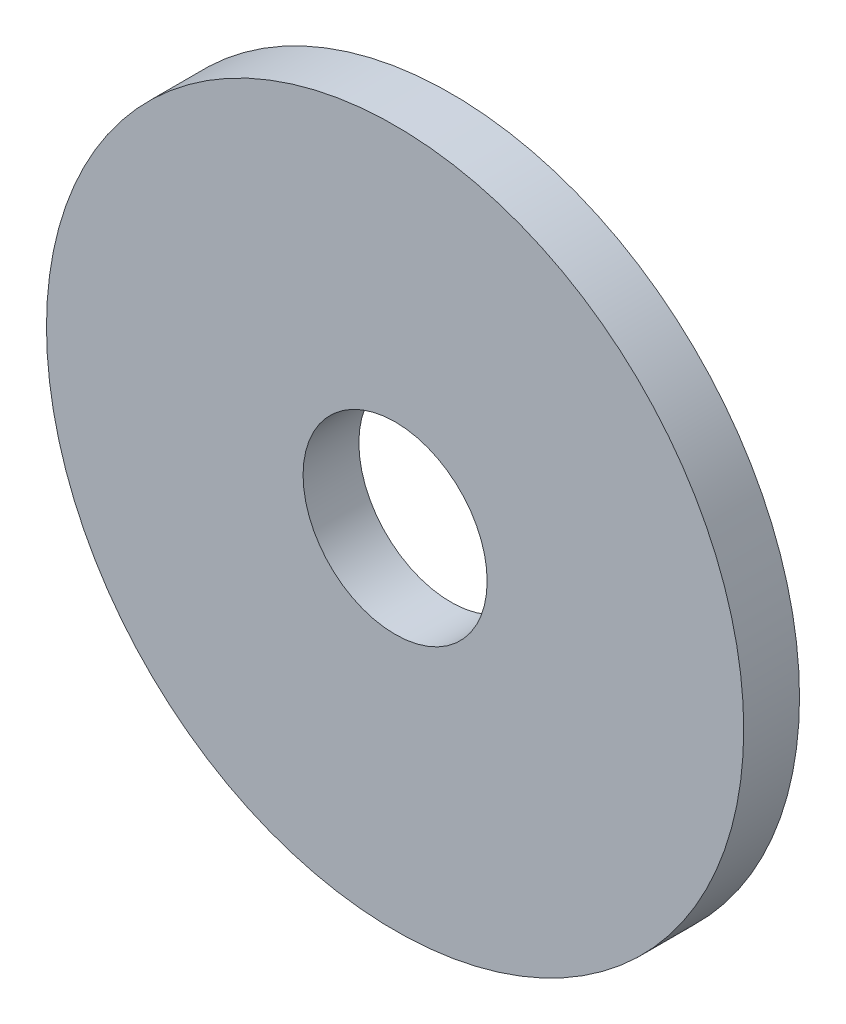
SolidWorks part; units mm, degrees
ref_plane "Plan de face" through (0, 0, 0) normal (0, 0, 1) x (1, 0, 0)
ref_plane "Plan de dessus" through (0, 0, 0) normal (0, 1, 0) x (1, 0, 0)
ref_plane "Plan de droite" through (0, 0, 0) normal (1, 0, 0) x (0, 0, -1)
sketch "Esquisse1" plane through (0, 0, 0) normal (0, 0, 1) x (1, 0, 0)
  circle A0 centre (0, 0) radius 12.5
  dimension "D1" = 25
extrude "Boss.-Extru.1" add sketch "Esquisse1" along normal blind 2
hole_wizard "Dégagement M61" positions "Esquisse2" profile "Esquisse3" hole size "M6" standard "ISO"
sketch "Esquisse2" plane through (0, 0, 0) normal (0, 0, -1) x (-1, 0, 0)
  point P0 (0, 0)
sketch "Esquisse3" plane through (0, 0, 0) normal (1, 0, 0) x (0, 1, 0)
  line L0 (0, 0) -> (0, 17.9828)
  line L1 (0, 17.9828) -> (3.3, 16)
  line L2 (3.3, 16) -> (3.3, 0)
  line L5 (3.3, 0) -> (0, 0)
  line L10 (0, 17.9828) -> (-3.3, 16) construction
  line L11 (0, -6.35) -> (0, 107.95) construction
  dimension "Diamètre du perçage" = 6.6
  dimension "Profondeur du perçage" = 16
  dimension "Angle de pointe" = 118
